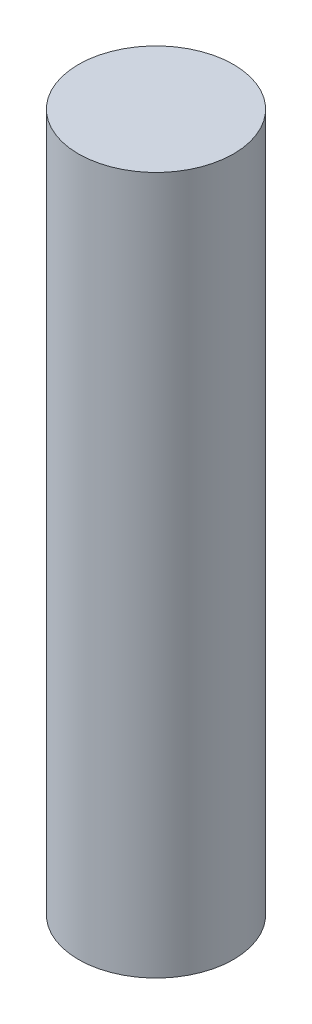
SolidWorks part; units mm, degrees
material "6061-T6 (SS)"
ref_plane "Front Plane" through (0, 0, 0) normal (0, 0, 1) x (1, 0, 0)
ref_plane "Top Plane" through (0, 0, 0) normal (0, 1, 0) x (1, 0, 0)
ref_plane "Right Plane" through (0, 0, 0) normal (1, 0, 0) x (0, 0, -1)
sketch "Sketch1" plane through (0, 0, 0) normal (0, 1, 0) x (1, 0, 0)
  circle A0 centre (0, 0) radius 3.175
  dimension "D1" = 6.35
extrude "Boss-Extrude1" add sketch "Sketch1" along normal blind 28.575
